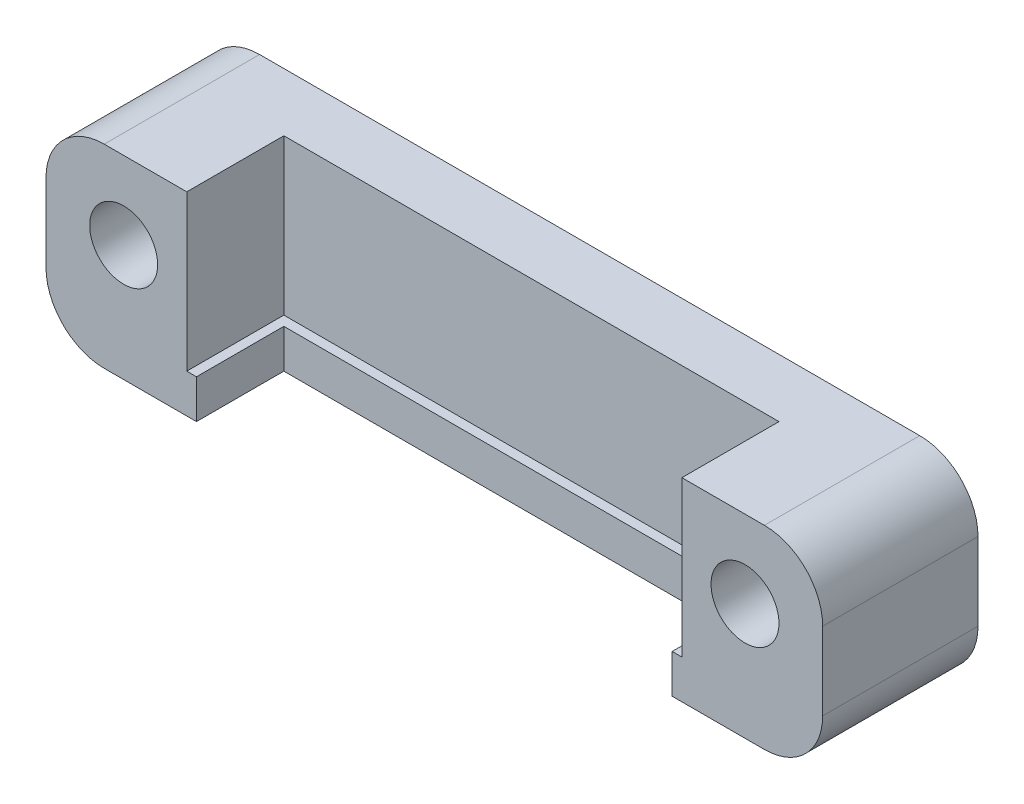
SolidWorks part; units mm, degrees
ref_plane "Front Plane" through (0, 0, 0) normal (0, 0, 1) x (1, 0, 0)
ref_plane "Top Plane" through (0, 0, 0) normal (0, 1, 0) x (1, 0, 0)
ref_plane "Right Plane" through (0, 0, 0) normal (1, 0, 0) x (0, 0, -1)
sketch "Sketch1" plane through (0, 0, 0) normal (0, 0, 1) x (1, 0, 0)
  line L1 (-17, 10) -> (17, 10)
  line L2 (-20, 7) -> (-20, 3)
  line L3 (-17, 0) -> (17, 0)
  line L4 (20, 7) -> (20, 3)
  circle A0 centre (-16, 6) radius 1.75
  circle A1 centre (16, 6) radius 1.75
  arc A2 (17, 10) -> (20, 7) centre (17, 7) cw
  arc A3 (17, 0) -> (20, 3) centre (17, 3) ccw
  arc A4 (-20, 3) -> (-17, 0) centre (-17, 3) ccw
  arc A5 (-17, 10) -> (-20, 7) centre (-17, 7) ccw
  dimension "D6" = 3.5
  dimension "D7" = 3
  dimension "D1" = 4
  dimension "D2" = 6
  dimension "D3" = 32
  dimension "D4" = 4
  dimension "D5" = 4
extrude "Boss-Extrude1" add sketch "Sketch1" along normal blind 8
sketch "Sketch2" plane through (0, 0, 8) normal (0, 0, 1) x (1, 0, 0)
  line L0 (17, 10) -> (-17, 10) construction
  line L1 (-12.75, 10) -> (12.75, 10)
  line L2 (-12.75, 10) -> (-12.75, 2)
  line L3 (-12.75, 2) -> (12.75, 2)
  line L4 (12.75, 10) -> (12.75, 2)
  line L5 (0, 2) -> (0, 0) construction
  dimension "D1" = 8
  dimension "D2" = 25.5
extrude "Cut-Extrude1" cut sketch "Sketch2" against normal blind 5
sketch "Sketch3" plane through (0, 2, 0) normal (0, 1, 0) x (1, 0, 0)
  line L0 (-12.75, -8) -> (12.75, -8) construction
  line L1 (-12.25, -8) -> (12.25, -8)
  line L2 (-12.25, -8) -> (-12.25, -3.5)
  line L3 (-12.25, -3.5) -> (12.25, -3.5)
  line L4 (12.25, -8) -> (12.25, -3.5)
  line L5 (-12.75, -3) -> (-12.75, -8) construction
  line L6 (-12.75, -3) -> (12.75, -3) construction
  line L7 (12.75, -3) -> (12.75, -8) construction
  dimension "D1" = 0.5
  dimension "D2" = 0.5
  dimension "D3" = 0.5
extrude "Cut-Extrude2" cut sketch "Sketch3" against normal through all
